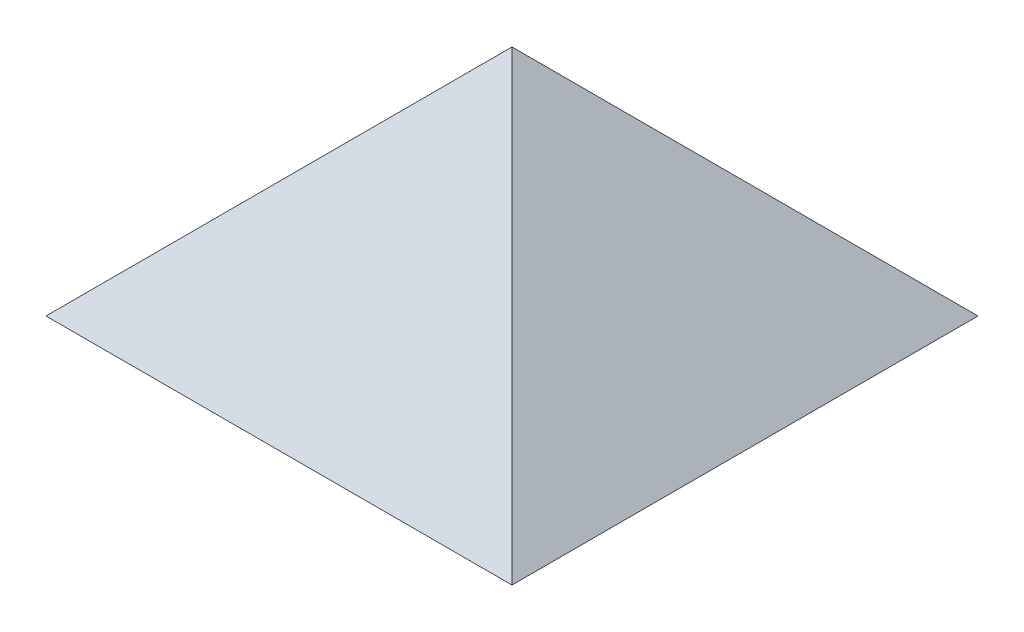
SolidWorks part; units mm, degrees
ref_plane "Front Plane" through (0, 0, 0) normal (0, 0, 1) x (1, 0, 0)
ref_plane "Top Plane" through (0, 0, 0) normal (0, 1, 0) x (1, 0, 0)
ref_plane "Right Plane" through (0, 0, 0) normal (1, 0, 0) x (0, 0, -1)
sketch "Sketch2" plane through (0, 0, 0) normal (0, 1, 0) x (1, 0, 0)
  line L1 (-25, -25) -> (25, -25)
  line L2 (-25, -25) -> (-25, 25)
  line L3 (-25, 25) -> (25, 25)
  line L4 (25, -25) -> (25, 25)
  line L5 (-25, -25) -> (25, 25) construction
  line L6 (-25, 25) -> (25, -25) construction
  point P0 (0, 0)
  dimension "D1" = 50
  dimension "D2" = 50
extrude "Boss-Extrude1" add sketch "Sketch2" along normal blind 50 draft 45
